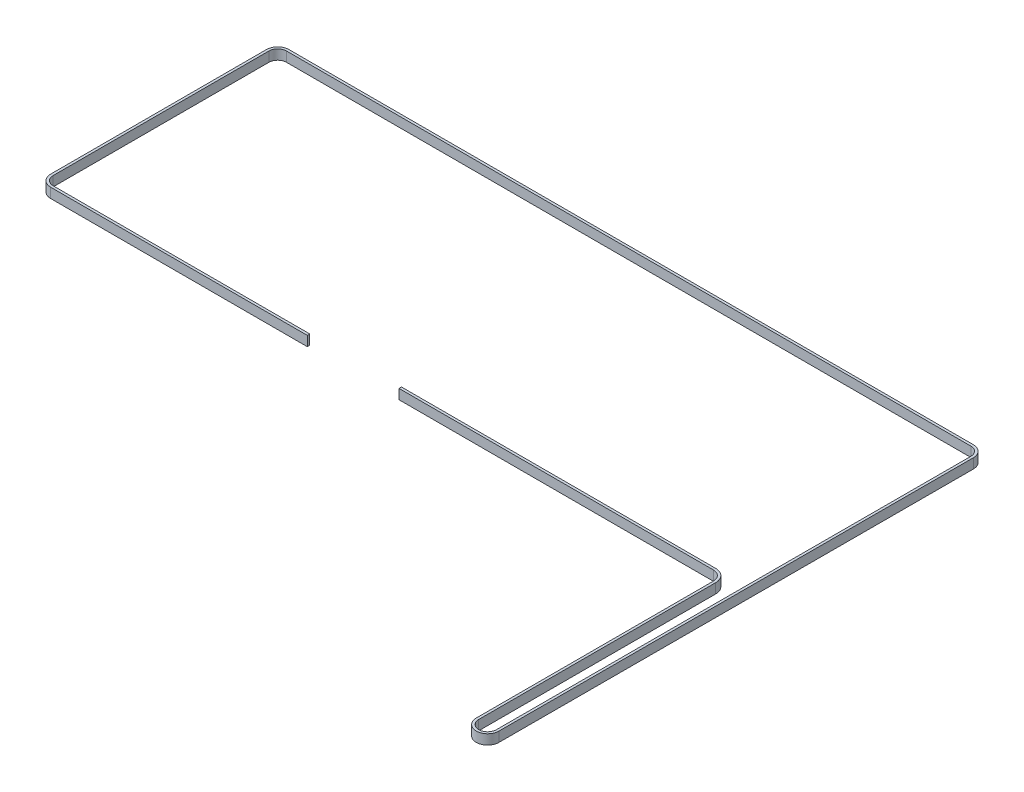
SolidWorks part; units mm, degrees
ref_plane "Front Plane" through (0, 0, 0) normal (0, 0, 1) x (1, 0, 0)
ref_plane "Top Plane" through (0, 0, 0) normal (0, 1, 0) x (1, 0, 0)
ref_plane "Right Plane" through (0, 0, 0) normal (1, 0, 0) x (0, 0, -1)
ref_plane "Plane1" through (0, 321, 0) normal (0, 1, 0) x (1, 0, 0)
sketch "Sketch1" plane through (0, 321, 0) normal (0, 1, 0) x (1, 0, 0)
  line L0 (195.6, 23.0073) -> (3.9749, 23.0073)
  line L1 (3.9749, 23.0073) -> (3.9749, 21.5073)
  line L2 (3.9749, 21.5073) -> (195.6, 21.5073)
  line L3 (201.6, 15.5073) -> (201.6, -129)
  line L4 (215.4, -129.0072) -> (215.7, 159.9928)
  line L5 (208.8, 166.9) -> (-208.5, 166.9)
  line L6 (-215.4, 160) -> (-215.4, 28.4573)
  line L7 (-208.5, 21.5573) -> (-52.0251, 21.5573)
  line L8 (-52.0251, 21.5573) -> (-52.0251, 23.0573)
  line L9 (-52.0251, 23.0573) -> (-208.5, 23.0573)
  line L10 (-213.9, 28.4573) -> (-213.9, 160)
  line L11 (-208.5, 165.4) -> (208.8, 165.4)
  line L12 (214.2, 159.9944) -> (213.9, -129.0056)
  line L13 (203.1, -129) -> (203.1, 15.5073)
  arc A0 (195.6, 21.5073) -> (201.6, 15.5073) centre (195.6, 15.5073) cw
  arc A1 (201.6, -129) -> (215.4, -129.0072) centre (208.5, -129) ccw
  arc A2 (215.7, 159.9928) -> (208.8, 166.9) centre (208.8, 160) ccw
  arc A3 (-208.5, 166.9) -> (-215.4, 160) centre (-208.5, 160) ccw
  arc A4 (-215.4, 28.4573) -> (-208.5, 21.5573) centre (-208.5, 28.4573) ccw
  arc A5 (-208.5, 23.0573) -> (-213.9, 28.4573) centre (-208.5, 28.4573) cw
  arc A6 (-213.9, 160) -> (-208.5, 165.4) centre (-208.5, 160) cw
  arc A7 (208.8, 165.4) -> (214.2, 159.9944) centre (208.8, 160) cw
  arc A8 (213.9, -129.0056) -> (203.1, -129) centre (208.5, -129) cw
  arc A9 (203.1, 15.5073) -> (195.6, 23.0073) centre (195.6, 15.5073) ccw
extrude "Boss-Extrude1" add sketch "Sketch1" against normal blind 6
